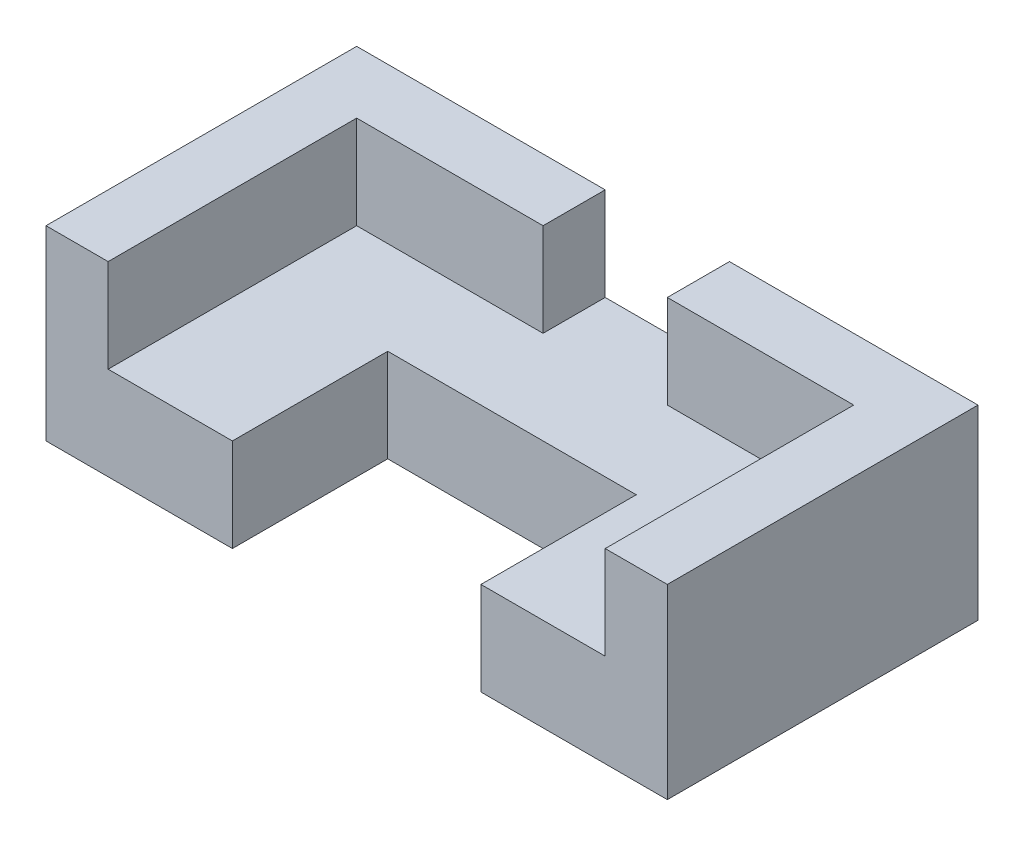
SolidWorks part; units mm, degrees
ref_plane "Front Plane" through (0, 0, 0) normal (0, 0, 1) x (1, 0, 0)
ref_plane "Top Plane" through (0, 0, 0) normal (0, 1, 0) x (1, 0, 0)
ref_plane "Right Plane" through (0, 0, 0) normal (1, 0, 0) x (0, 0, -1)
sketch "Sketch1" plane through (0, 0, 0) normal (0, 1, 0) x (1, 0, 0)
  line L0 (0, 0) -> (30, 0)
  line L1 (30, 0) -> (30, 25)
  line L2 (30, 25) -> (70, 25)
  line L3 (70, 25) -> (70, 0)
  line L4 (70, 0) -> (100, 0)
  line L5 (100, 0) -> (100, 50)
  line L6 (100, 50) -> (0, 50)
  line L7 (0, 50) -> (0, 0)
  dimension "D1" = 100
  dimension "D2" = 30
  dimension "D3" = 30
  dimension "D4" = 50
  dimension "D5" = 25
extrude "Boss-Extrude1" add sketch "Sketch1" along normal blind 15
sketch "Sketch2" plane through (0, 15, 0) normal (0, 1, 0) x (1, 0, 0)
  line L0 (0, 0) -> (10, 0)
  line L1 (0, 0) -> (30, 0) construction
  line L2 (10, 0) -> (10, 40)
  line L3 (10, 40) -> (90, 40)
  line L4 (90, 40) -> (90, 0)
  line L5 (70, 0) -> (100, 0) construction
  line L6 (90, 0) -> (100, 0)
  line L7 (100, 0) -> (100, 50)
  line L8 (100, 50) -> (0, 50)
  line L9 (100, 50) -> (0, 50) construction
  line L10 (0, 50) -> (0, 0) construction
  line L11 (0, 50) -> (0, 0)
  dimension "D1" = 80
  dimension "D2" = 10
  dimension "D3" = 40
extrude "Boss-Extrude2" add sketch "Sketch2" along normal blind 15
sketch "Sketch3" plane through (0, 30, 0) normal (0, 1, 0) x (1, 0, 0)
  line L0 (40, 40) -> (40, 50)
  line L1 (10, 40) -> (90, 40) construction
  line L2 (100, 50) -> (0, 50) construction
  line L3 (40, 50) -> (60, 50)
  line L4 (60, 50) -> (60, 40)
  line L5 (60, 40) -> (40, 40)
  point P8 (60, 45)
  dimension "D1" = 20
  dimension "D2" = 40
extrude "Cut-Extrude1" cut sketch "Sketch3" against normal blind 15
